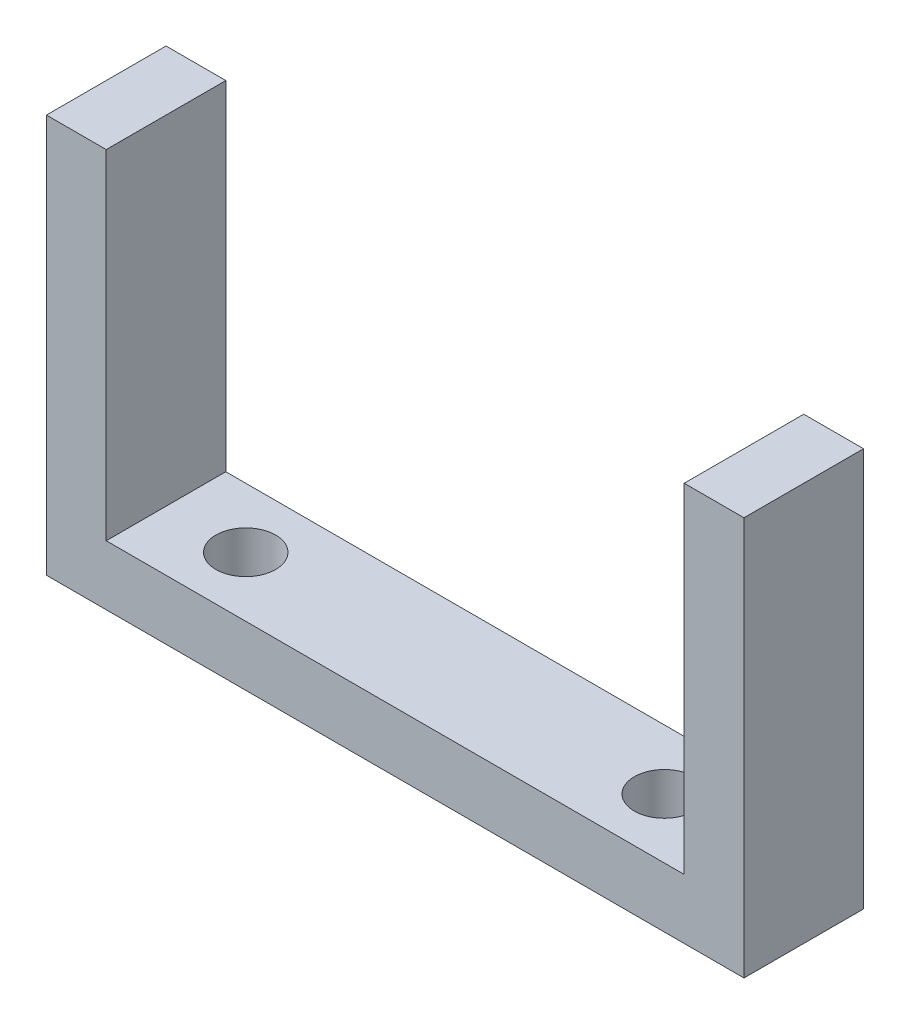
SolidWorks part; units mm, degrees
ref_plane "Front Plane" through (0, 0, 0) normal (0, 0, 1) x (1, 0, 0)
ref_plane "Top Plane" through (0, 0, 0) normal (0, 1, 0) x (1, 0, 0)
ref_plane "Right Plane" through (0, 0, 0) normal (1, 0, 0) x (0, 0, -1)
sketch "Sketch1" plane through (0, 0, 0) normal (0, 0, 1) x (1, 0, 0)
  line L0 (-32, 0) -> (-35, 0)
  line L1 (0, 0) -> (-3, 0)
  line L2 (0, 0) -> (0, -20)
  line L3 (0, -20) -> (-35, -20)
  line L4 (-35, 0) -> (-35, -20)
  line L6 (-3, 0) -> (-3, -17)
  line L7 (-3, -17) -> (-32, -17)
  line L8 (-32, 0) -> (-32, -17)
  dimension "D1" = 3
  dimension "D2" = 3
  dimension "D3" = 3
  dimension "D4" = 20
  dimension "D5" = 35
extrude "Boss-Extrude1" add sketch "Sketch1" along normal blind 6
sketch "Sketch2" plane through (0, -20, 0) normal (0, -1, 0) x (1, 0, 0)
  circle A0 centre (-28, 3) radius 1.5
  circle A1 centre (-7, 3) radius 1.5
  point P4 (0, 0)
  point P5 (0, 0)
  point P6 (0, 0)
extrude "Cut-Extrude1" cut sketch "Sketch2" against normal blind 3
